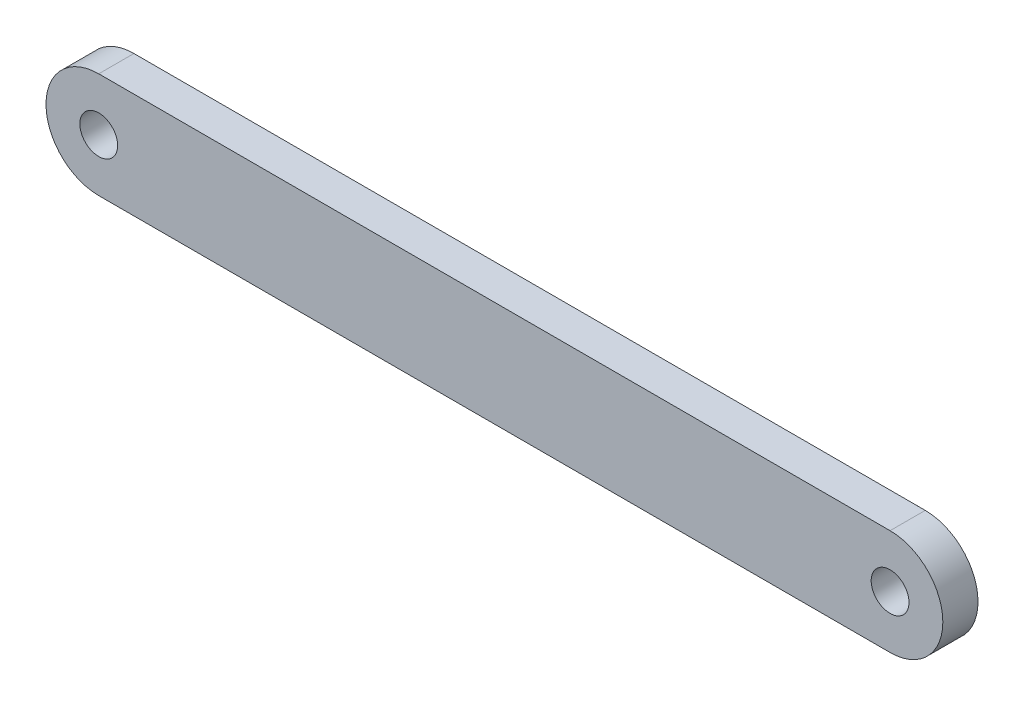
SolidWorks part; units mm, degrees
material "A-玻璃纤维"
ref_plane "前视基准面" through (0, 0, 0) normal (0, 0, 1) x (1, 0, 0)
ref_plane "上视基准面" through (0, 0, 0) normal (0, 1, 0) x (1, 0, 0)
ref_plane "右视基准面" through (0, 0, 0) normal (1, 0, 0) x (0, 0, -1)
sketch "草图1" plane through (0, 0, 0) normal (0, 0, 1) x (1, 0, 0)
  line L0 (0, 0) -> (90, 0) construction
  line L1 (0, 6) -> (90, 6)
  line L2 (0, -6) -> (90, -6)
  arc A0 (0, 6) -> (0, -6) centre (0, 0) ccw
  arc A1 (90, -6) -> (90, 6) centre (90, 0) ccw
  circle A2 centre (0, 0) radius 2.15
  circle A3 centre (90, 0) radius 2.15
  point P3 (45, 0)
  dimension "D2" = 4.3
  dimension "D3" = 6
  dimension "D1" = 90
extrude "凸台-拉伸1" add sketch "草图1" along normal blind 4
